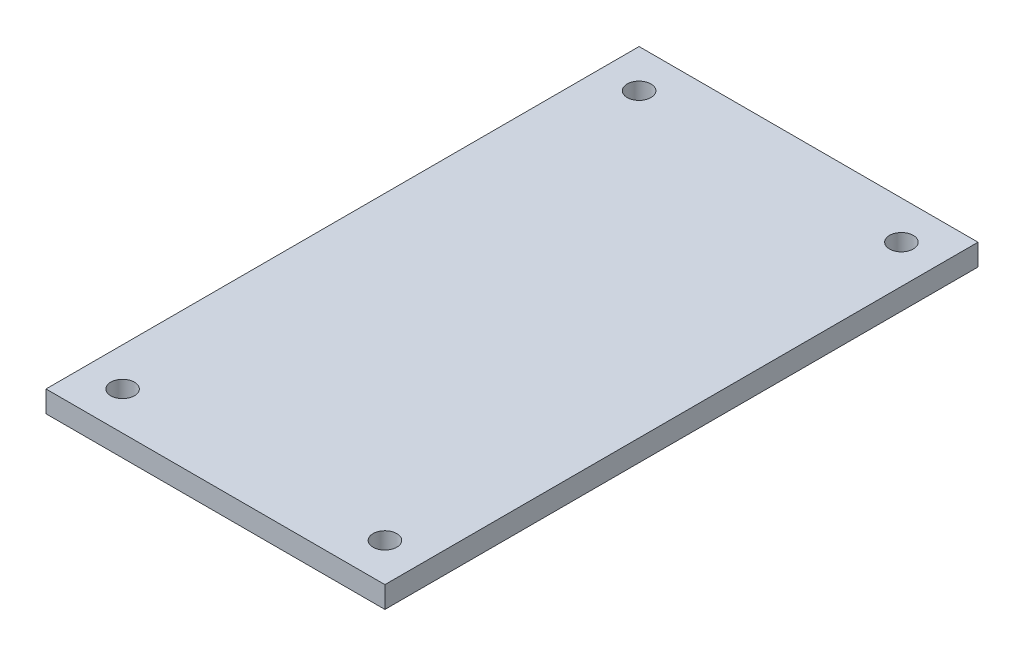
SolidWorks part; units mm, degrees
ref_plane "Front Plane" through (0, 0, 0) normal (0, 0, 1) x (1, 0, 0)
ref_plane "Top Plane" through (0, 0, 0) normal (0, 1, 0) x (1, 0, 0)
ref_plane "Right Plane" through (0, 0, 0) normal (1, 0, 0) x (0, 0, -1)
sketch "Sketch1" plane through (0, 0, 0) normal (0, 1, 0) x (1, 0, 0)
  line L0 (-11.3, -163.7) -> (-11.3, -11.3) construction
  line L1 (-100, 0) -> (0, 0)
  line L2 (-100, 0) -> (-100, -175)
  line L3 (-100, -175) -> (0, -175)
  line L4 (0, 0) -> (0, -175)
  circle A0 centre (-88.7, -163.7) radius 3.5
  circle A1 centre (-11.3, -163.7) radius 3.5
  circle A2 centre (-11.3, -11.3) radius 3.5
  circle A3 centre (-88.7, -11.3) radius 3.5
  point P13 (-11.3, -87.5)
  point P14 (0, -87.5)
  dimension "D3" = 7
  dimension "D4" = 77.4
  dimension "D5" = 152.4
  dimension "D1" = 175
  dimension "D2" = 11.3
  dimension "D6" = 11.3
extrude "Boss-Extrude1" add sketch "Sketch1" along normal blind 6.35
